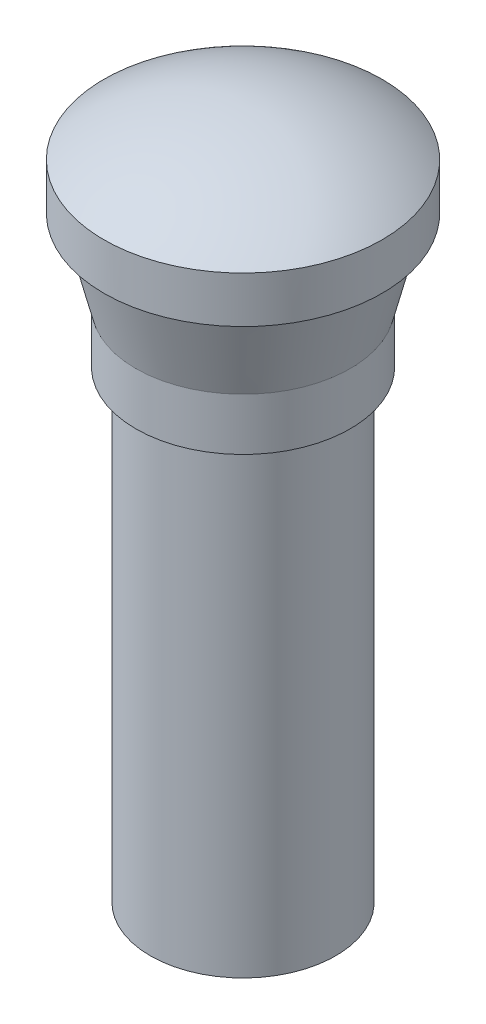
SolidWorks part; units mm, degrees
ref_plane "Plan de face" through (0, 0, 0) normal (0, 0, 1) x (1, 0, 0)
ref_plane "Plan de dessus" through (0, 0, 0) normal (0, 1, 0) x (1, 0, 0)
ref_plane "Plan de droite" through (0, 0, 0) normal (1, 0, 0) x (0, 0, -1)
sketch "Esquisse1" plane through (0, 0, 0) normal (0, 0, 1) x (1, 0, 0)
  line L0 (0, 0) -> (8, 0)
  line L1 (8, 0) -> (8, 40)
  line L2 (8, 40) -> (9.25, 40)
  line L3 (9.25, 40) -> (9.25, 44.5)
  line L4 (9.25, 44.5) -> (11, 51.5)
  line L5 (11, 51.5) -> (12, 51.5)
  line L6 (0, 0) -> (0, 55.5) construction
  line L7 (12, 51.5) -> (12, 55.5)
  line L8 (0, 0) -> (0, 59.5)
  arc A0 (12, 55.5) -> (0, 59.5) centre (0, 39.5) ccw
  dimension "D3" = 9.25
  dimension "D1" = 8
  dimension "D2" = 4
  dimension "D4" = 12
  dimension "D5" = 11
  dimension "D6" = 40
  dimension "D7" = 4.5
  dimension "D8" = 7
  dimension "D9" = 4
revolve "Révolution1" add sketch "Esquisse1" angle 360 about L6
